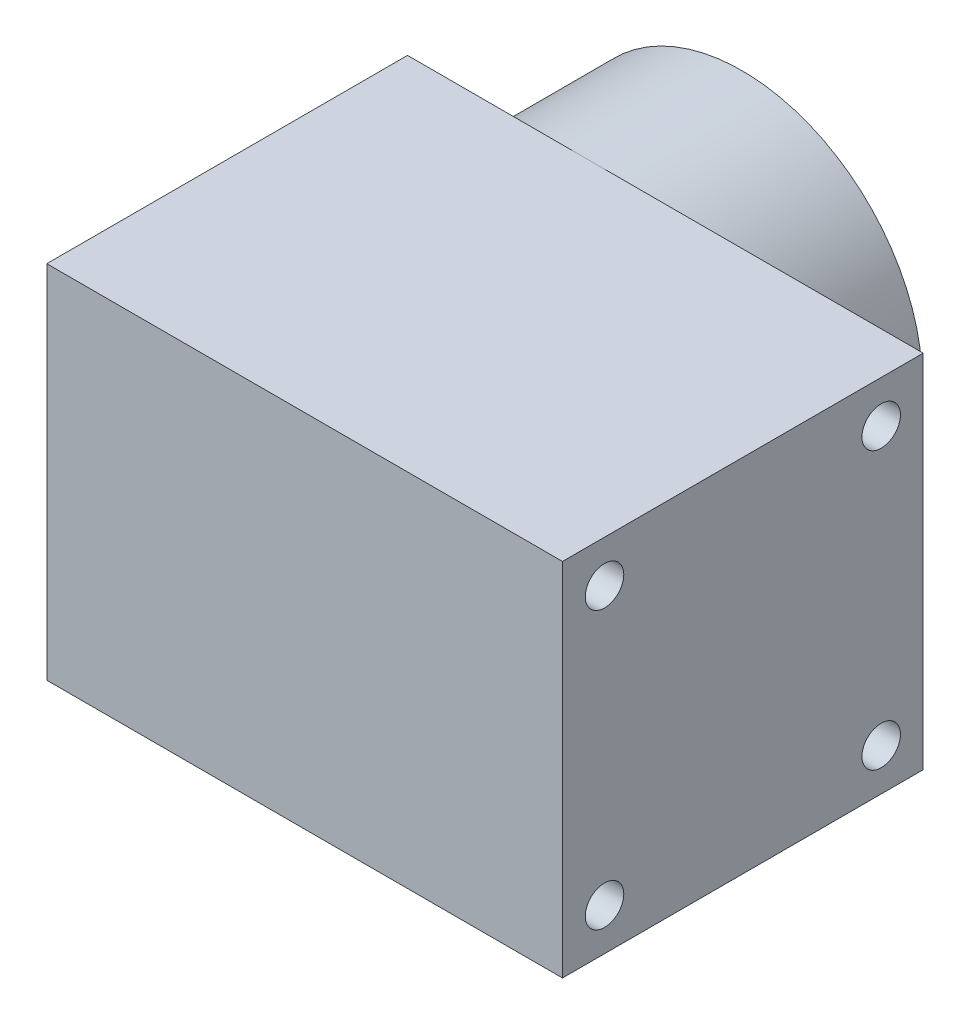
SolidWorks part; units mm, degrees
ref_plane "Front Plane" through (0, 0, 0) normal (0, 0, 1) x (1, 0, 0)
ref_plane "Top Plane" through (0, 0, 0) normal (0, 1, 0) x (1, 0, 0)
ref_plane "Right Plane" through (0, 0, 0) normal (1, 0, 0) x (0, 0, -1)
sketch "Sketch1" plane through (0, 0, 0) normal (0, 0, 1) x (1, 0, 0)
  circle A0 centre (0, 0) radius 28.1
extrude "Boss-Extrude2" add sketch "Sketch1" along normal blind 24
sketch "Sketch3" plane through (0, 0, 0) normal (0, 0, -1) x (-1, 0, 0)
  line L2 (-1.6618, 2.5) -> (1.6618, 2.5)
  arc A1 (-1.6618, 2.5) -> (1.6618, 2.5) centre (0, 0) ccw
extrude "Cut-Extrude2" cut sketch "Sketch3" against normal blind 21.5
sketch "Sketch4" plane through (0, 0, 0) normal (0, 0, -1) x (-1, 0, 0)
  circle A0 centre (0, 0) radius 3
extrude "Cut-Extrude3" cut sketch "Sketch4" against normal blind 9.5
sketch "Sketch6" plane through (0, 0, 0) normal (0, 0, -1) x (-1, 0, 0)
  circle A0 centre (0, 0) radius 6.025
extrude "Cut-Extrude4" cut sketch "Sketch6" against normal blind 6.2
sketch "Sketch7" plane through (0, 0, 24) normal (0, 0, 1) x (1, 0, 0)
  line L1 (-28.1, -28.1) -> (28.1, -28.1)
  line L2 (-28.1, -28.1) -> (-28.1, 28.1)
  line L3 (-28.1, 28.1) -> (28.1, 28.1)
  line L4 (28.1, -28.1) -> (28.1, 28.1)
  line L5 (-28.1, -28.1) -> (28.1, 28.1) construction
  line L6 (-28.1, 28.1) -> (28.1, -28.1) construction
  point P0 (0, 0)
extrude "Boss-Extrude3" add sketch "Sketch7" along normal blind 56.2
sketch "Sketch8" plane through (28.1, 0, 0) normal (1, 0, 0) x (0, 0, -1)
  line L0 (-80.2, 28.1) -> (-24, 28.1) construction
  line L1 (-80.2, 28.1) -> (-24, 28.1)
  line L2 (-80.2, 28.1) -> (-80.2, -28.1)
  line L3 (-80.2, -28.1) -> (-24, -28.1)
  line L4 (-24, 28.1) -> (-24, -28.1)
  line L5 (-80.2, -28.1) -> (-80.2, 28.1) construction
extrude "Boss-Extrude4" add sketch "Sketch8" along normal blind 14.14
sketch "Sketch10" plane through (42.24, 0, 0) normal (1, 0, 0) x (0, 0, -1)
  line L1 (-80.2, 28.1) -> (-24, 28.1)
  line L2 (-80.2, 28.1) -> (-80.2, -28.1)
  line L3 (-80.2, -28.1) -> (-24, -28.1)
  line L4 (-24, 28.1) -> (-24, -28.1)
extrude "Boss-Extrude5" add sketch "Sketch10" along normal blind 10
sketch "Sketch11" plane through (0, 0, 80.2) normal (0, 0, 1) x (1, 0, 0)
  line L1 (52.24, 28.1) -> (-28.1, 28.1) construction
  line L3 (42.24, 28.1) -> (52.24, 28.1)
  line L4 (42.24, 28.1) -> (42.24, -28.1)
  line L5 (42.24, -28.1) -> (52.24, -28.1)
  line L6 (52.24, 28.1) -> (52.24, -28.1)
sketch "Sketch19" plane through (-28.1, 0, 0) normal (-1, 0, 0) x (0, 0, 1)
  line L7 (26.5, 25.6) -> (77.7, 25.6)
  line L8 (26.5, 25.6) -> (26.5, -25.6)
  line L9 (26.5, -25.6) -> (77.7, -25.6)
  line L10 (77.7, 25.6) -> (77.7, -25.6)
extrude "Cut-Extrude5" cut sketch "Sketch19" against normal blind 63.7
sketch "Sketch20" plane through (0, 0, 0) normal (0, 0, -1) x (-1, 0, 0)
  arc A1 (0, 15) -> (-15, 0) centre (0, 0) ccw
sketch3d "3DSketch2"
  line L2 (0, 15, 0) -> (0, 22.5, 0)
  line L3 (0, 15, 0) -> (0, 15, 42.1431)
  line L4 (0, 15, 42.1431) -> (0, 22.5, 42.1431)
  line L5 (0, 22.5, 0) -> (0, 22.5, 42.1431)
  arc A0 (0, 15, 0) -> (15, 0, 0) centre (0, 0, 0) ccw construction
  point P10 (0, 0, -15)
sweep "Cut-Sweep2" cut profiles "3DSketch2" path "Sketch20"
sketch "Sketch21" plane through (52.24, 0, 0) normal (1, 0, 0) x (0, 0, -1)
  circle A0 centre (-73.65, 21.55) radius 3
  circle A1 centre (-30.55, 21.55) radius 3
  circle A2 centre (-30.55, -21.55) radius 3
  circle A3 centre (-73.65, -21.55) radius 3
extrude "Cut-Extrude7" cut sketch "Sketch21" against normal blind 20
